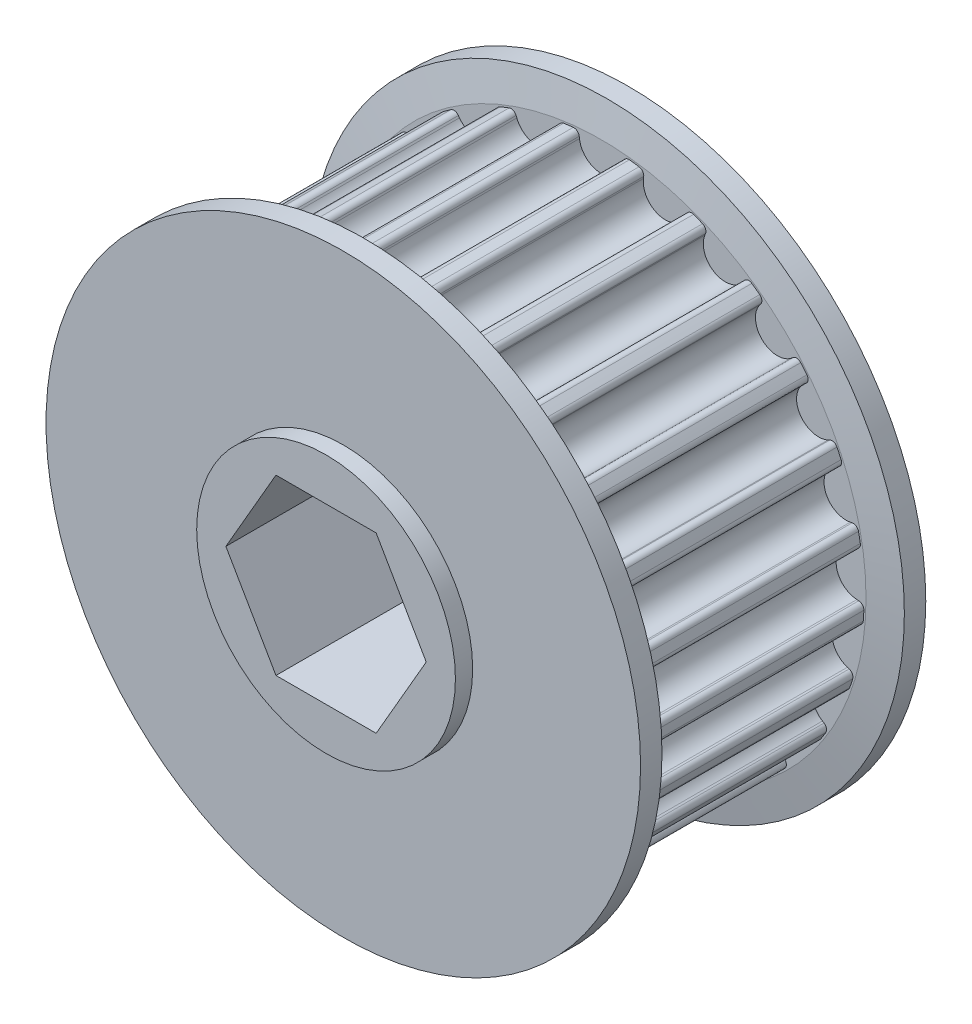
SolidWorks part; units mm, degrees
material "PETG"
ref_plane "Front Plane" through (0, 0, 0) normal (0, 0, 1) x (1, 0, 0)
ref_plane "Top Plane" through (0, 0, 0) normal (0, 1, 0) x (1, 0, 0)
ref_plane "Right Plane" through (0, 0, 0) normal (1, 0, 0) x (0, 0, -1)
sketch "Sketch2" plane through (0, 0, 0) normal (0, 0, 1) x (1, 0, 0)
  circle A0 centre (0, 0) radius 19.3468
  dimension "D1" = 38.6936
extrude "pulley" add sketch "Sketch2" along normal mid plane 17
sketch "tooth" plane through (0, 0, 0) normal (0, 0, 1) x (1, 0, 0)
  line L0 (0, 0) -> (0, 18.9468) construction
  line L1 (4.9563, 18.2871) -> (0, 18.9468) construction
  line L2 (4.9563, 18.2871) -> (0, 0) construction
  line L3 (-2.1327, 22.9824) -> (-1.6129, 18.7488)
  line L6 (2.1327, 22.9824) -> (1.6129, 18.7488)
  line L7 (-2.1327, 22.9824) -> (2.1327, 22.9824)
  arc A1 (-1.6129, 18.7488) -> (1.6129, 18.7488) centre (0, 18.9468) ccw
  arc A2 (0, 18.9468) -> (4.9563, 18.2871) centre (0, 0) cw construction
  circle A3 centre (4.9563, 18.2871) radius 1.625 construction
  dimension "D1" = 18.9468
  dimension "D2" = 3.25
  dimension "D3" = 5
  dimension "D5" = 14
extrude "cut tooth" cut sketch "tooth" against normal mid plane 17
fillet "blend tooth" radius 0.4 2 edges at (1.6774, 19.274, 0) (-1.6774, 19.274, 0)
pattern_circular "tooth pattern" count 25 over 360 about axis through (0, 0, 0) along (0, 0, 1) of "cut tooth", "blend tooth"
sketch "Sketch3" plane through (0, 0, 0) normal (0, 0, 1) x (1, 0, 0)
  circle A0 centre (0, 0) radius 21.8868
  circle A1 centre (0, 0) radius 19.3468 construction
  dimension "D1" = 2.54
extrude "sidewall" add sketch "Sketch3" along normal blind 2 from offset 8.5
mirror "mirror sidewall" about plane through (0, 0, 0) normal (0, 0, 1) of "sidewall"
chamfer "sidewall chamfer" distance 2.4 angle 10 2 edges at (21.8868, 0, 8.5) (21.8868, 0, -8.5)
sketch "Sketch5" plane through (0, 0, 0) normal (0, 0, 1) x (1, 0, 0)
  circle A0 centre (0, 0) radius 9.525
  dimension "D1" = 19.05
extrude "bearing spacer (Manual Suppress)" add sketch "Sketch5" along normal blind 11.77 and the other way blind 11.77
sketch "Sketch4" plane through (0, 0, 0) normal (0, 0, 1) x (1, 0, 0)
  line L1 (3.6882, 6.3881) -> (-3.6882, 6.3881)
  line L2 (-3.6882, 6.3881) -> (-7.3763, 0)
  line L3 (-7.3763, 0) -> (-3.6882, -6.3881)
  line L4 (-3.6882, -6.3881) -> (3.6882, -6.3881)
  line L5 (3.6882, -6.3881) -> (7.3763, 0)
  line L6 (7.3763, 0) -> (3.6882, 6.3881)
  circle A0 centre (0, 0) radius 6.3881 construction
  dimension "D1" = 12.7762
extrude "hex shaft" cut sketch "Sketch4" against normal mid plane 127
equation "\"INPUT_pulley_teeth\"= 25"
equation "\"pulley_c2c\"= 5mm"
equation "\"pulley_teeth_deg\"= 360 / \"INPUT_pulley_teeth\""
equation "\"pulley_radius\"= ( \"pulley_c2c\" / ( 2 * cos ( \"iso_half_angle\" ) ) ) - 1mm"
equation "\"iso_half_angle\"= ( 180 - \"pulley_teeth_deg\" ) / 2"
equation "\"D1@tooth\" = \"pulley_radius\""
equation "\"pulley_tooth_dia\"= 3.25mm"
equation "\"D3@tooth\"=\"pulley_c2c\""
equation "\"D2@tooth\"=\"pulley_tooth_dia\""
equation "\"D1@Sketch2\"=2* \"pulley_radius\"+\"pulley_tooth_offset\""
equation "\"pulley_tooth_offset\"= .8mm"
equation "\"D1@tooth pattern\" = \"INPUT_pulley_teeth\""
equation "\"INPUT_pulley_belt_9_or_15_(unitless)\"= 15"
equation "\"D1@pulley\"=\"pulley_width\""
equation "\"D19@sidewall\"= ( \"pulley_width\" / 2 )"
equation "\"D1@sidewall\"=\"pulley_sidewall_thick\""
equation "\"pulley_width\"= 17mm"
equation "\"D1@cut tooth\"=\"pulley_width\""
equation "\"D1@sidewall chamfer\" = 2.4mm"
equation "\"D1@bearing spacer (Manual Suppress)\" = 0.05 +  ( \"pulley_width\" / 2 )  + \"pulley_sidewall_thick\""
equation "\"D2@bearing spacer (Manual Suppress)\" = 0.05 +  ( \"pulley_width\" / 2 )  + \"pulley_sidewall_thick\""
equation "\"pulley_sidewall_thick\"= 2mm"
equation "\"D1\"= \"pulley_width\""
equation "\"D19\"= ( \"pulley_width\" / 2 ) + \"pulley_sidewall_thick\" - 0.02mm"
equation "\"rad_len\" = \"INPUT_pulley_teeth\" * \"pulley_c2c\""
